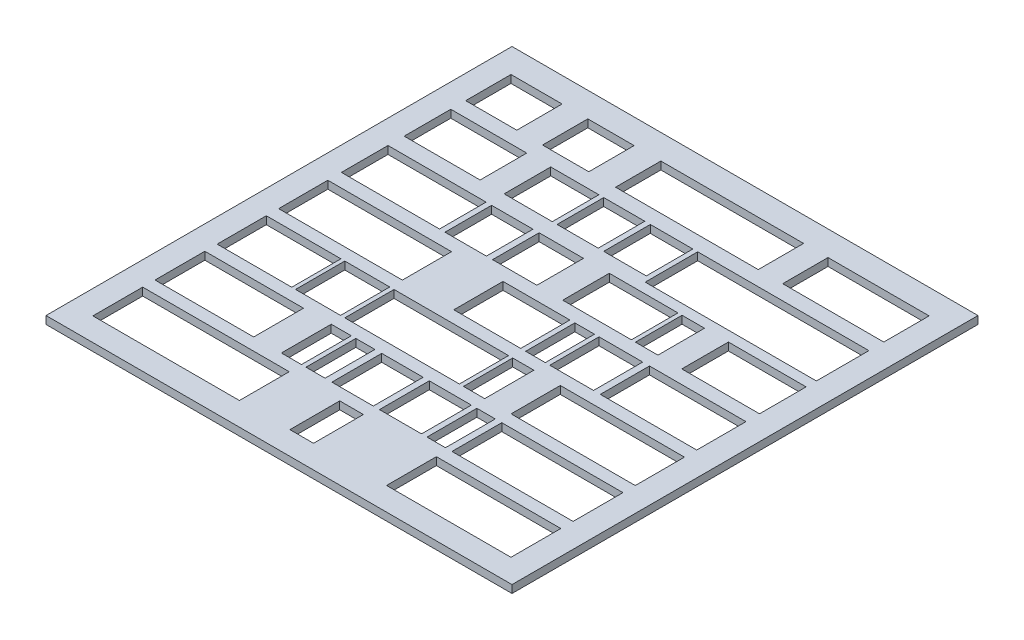
SolidWorks part; units mm, degrees
material "Maple"
ref_plane "Front Plane" through (0, 0, 0) normal (0, 0, 1) x (1, 0, 0)
ref_plane "Top Plane" through (0, 0, 0) normal (0, 1, 0) x (1, 0, 0)
ref_plane "Right Plane" through (0, 0, 0) normal (1, 0, 0) x (0, 0, -1)
sketch "Sketch1" plane through (0, 0, 0) normal (0, 1, 0) x (1, 0, 0)
  line L0 (-95.25, 95.25) -> (95.25, -95.25) construction
  line L1 (-95.25, 95.25) -> (95.25, 95.25)
  line L2 (-95.25, 95.25) -> (-95.25, -95.25)
  line L3 (-95.25, -95.25) -> (95.25, -95.25)
  line L4 (95.25, 95.25) -> (95.25, -95.25)
  dimension "D1" = 190.5
extrude "Boss-Extrude1" add sketch "Sketch1" along normal blind 3.175
sketch "Sketch4" plane through (0, 3.175, 0) normal (0, 1, 0) x (1, 0, 0)
  line L4 (-85.5388, 66.6005) -> (-64.6368, 66.6005)
  line L5 (-64.6368, 66.6005) -> (-64.6368, 85.1213)
  line L6 (-64.6368, 85.1213) -> (-85.5388, 85.1213)
  line L7 (-85.5388, 85.1213) -> (-85.5388, 66.6005)
  line L8 (-54.1196, 66.6005) -> (-35.202, 66.6005)
  line L9 (-35.202, 66.6005) -> (-35.202, 85.1213)
  line L10 (-35.202, 85.1213) -> (-54.1196, 85.1213)
  line L11 (-54.1196, 85.1213) -> (-54.1196, 66.6005)
  line L12 (-24.2702, 66.6005) -> (34.0704, 66.6005)
  line L13 (34.0704, 66.6005) -> (34.0704, 85.1213)
  line L14 (34.0704, 85.1213) -> (-24.2702, 85.1213)
  line L15 (-24.2702, 85.1213) -> (-24.2702, 66.6005)
  line L16 (44.0592, 66.6003) -> (85.382, 66.6003)
  line L17 (85.382, 66.6003) -> (85.382, 85.1213)
  line L18 (85.382, 85.1213) -> (44.0592, 85.1213)
  line L19 (44.0592, 85.1213) -> (44.0592, 66.6003)
  line L20 (-85.5388, 41.4648) -> (-54.4982, 41.4648)
  line L21 (-54.4982, 41.4648) -> (-54.4982, 60.515)
  line L22 (-54.4982, 60.515) -> (-85.5388, 60.515)
  line L23 (-85.5388, 60.515) -> (-85.5388, 41.4648)
  line L24 (-44.6805, 41.4648) -> (-24.9971, 41.4648)
  line L25 (-24.9971, 41.4648) -> (-24.9971, 60.515)
  line L26 (-24.9971, 60.515) -> (-44.6805, 60.515)
  line L27 (-44.6805, 60.515) -> (-44.6805, 41.4648)
  line L28 (-23.0273, 41.4648) -> (-6.2263, 41.4648)
  line L29 (-6.2263, 41.4648) -> (-6.2263, 60.515)
  line L30 (-6.2263, 60.515) -> (-23.0273, 60.515)
  line L31 (-23.0273, 60.515) -> (-23.0273, 41.4648)
  line L32 (-3.9772, 41.4648) -> (13.4192, 41.4648)
  line L33 (13.4192, 41.4648) -> (13.4192, 60.515)
  line L34 (13.4192, 60.515) -> (-3.9772, 60.515)
  line L35 (-3.9772, 60.515) -> (-3.9772, 41.4648)
  line L36 (15.4036, 39.0476) -> (85.382, 39.0476)
  line L37 (85.382, 39.0476) -> (85.382, 60.515)
  line L38 (85.382, 60.515) -> (15.4036, 60.515)
  line L39 (15.4036, 60.515) -> (15.4036, 39.0476)
  line L40 (34.661, 15.8004) -> (43.8468, 15.8004)
  line L41 (43.8468, 15.8004) -> (43.8468, 34.8504)
  line L42 (43.8468, 34.8504) -> (34.661, 34.8504)
  line L43 (34.661, 34.8504) -> (34.661, 15.8004)
  line L44 (-85.5388, 15.8004) -> (-45.4502, 15.8004)
  line L45 (-45.4502, 15.8004) -> (-45.4502, 34.8504)
  line L46 (-45.4502, 34.8504) -> (-85.5388, 34.8504)
  line L47 (-85.5388, 34.8504) -> (-85.5388, 15.8004)
  line L48 (-43.2012, 15.8004) -> (-26.2678, 15.8004)
  line L49 (-26.2678, 15.8004) -> (-26.2678, 34.8504)
  line L50 (-26.2678, 34.8504) -> (-43.2012, 34.8504)
  line L51 (-43.2012, 34.8504) -> (-43.2012, 15.8004)
  line L52 (-23.7543, 15.8004) -> (-5.6303, 15.8004)
  line L53 (-5.6303, 15.8004) -> (-5.6303, 34.8504)
  line L54 (-5.6303, 34.8504) -> (-23.7543, 34.8504)
  line L55 (-23.7543, 34.8504) -> (-23.7543, 15.8004)
  line L56 (4.9289, 15.8004) -> (32.9989, 15.8004)
  line L57 (32.9989, 15.8004) -> (32.9989, 34.8504)
  line L58 (32.9989, 34.8504) -> (4.9289, 34.8504)
  line L59 (4.9289, 34.8504) -> (4.9289, 15.8004)
  line L60 (53.6122, 15.8004) -> (85.382, 15.8004)
  line L61 (85.382, 15.8004) -> (85.382, 34.8504)
  line L62 (85.382, 34.8504) -> (53.6122, 34.8504)
  line L63 (53.6122, 34.8504) -> (53.6122, 15.8004)
  line L64 (-85.5388, -9.8641) -> (-34.9574, -9.8641)
  line L65 (-34.9574, -9.8641) -> (-34.9574, 10.2441)
  line L66 (-34.9574, 10.2441) -> (-85.5388, 10.2441)
  line L67 (-85.5388, 10.2441) -> (-85.5388, -9.8641)
  line L68 (-13.9229, -9.8641) -> (13.4195, -9.8641)
  line L69 (13.4195, -9.8641) -> (13.4195, 10.2441)
  line L70 (13.4195, 10.2441) -> (-13.9229, 10.2441)
  line L71 (-13.9229, 10.2441) -> (-13.9229, -9.8641)
  line L72 (15.4458, -9.8641) -> (23.4738, -9.8641)
  line L73 (23.4738, -9.8641) -> (23.4738, 10.2441)
  line L74 (23.4738, 10.2441) -> (15.4458, 10.2441)
  line L75 (15.4458, 10.2441) -> (15.4458, -9.8641)
  line L76 (45.9634, -9.8641) -> (85.382, -9.8641)
  line L77 (85.382, -9.8641) -> (85.382, 10.2441)
  line L78 (85.382, 10.2441) -> (45.9634, 10.2441)
  line L79 (45.9634, 10.2441) -> (45.9634, -9.8641)
  line L80 (25.3259, -9.8641) -> (43.1853, -9.8641)
  line L81 (43.1853, -9.8641) -> (43.1853, 10.2441)
  line L82 (43.1853, 10.2441) -> (25.3259, 10.2441)
  line L83 (25.3259, 10.2441) -> (25.3259, -9.8641)
  line L84 (-85.5388, -34.9997) -> (-55.0418, -34.9997)
  line L85 (-55.0418, -34.9997) -> (-55.0418, -14.8913)
  line L86 (-55.0418, -14.8913) -> (-85.5388, -14.8913)
  line L87 (-85.5388, -14.8913) -> (-85.5388, -34.9997)
  line L88 (-53.4782, -34.9997) -> (-35.09, -34.9997)
  line L89 (-35.09, -34.9997) -> (-35.09, -14.8913)
  line L90 (-35.09, -14.8913) -> (-53.4782, -14.8913)
  line L91 (-53.4782, -14.8913) -> (-53.4782, -34.9997)
  line L92 (-33.3458, -34.9997) -> (13.4858, -34.9997)
  line L93 (13.4858, -34.9997) -> (13.4858, -14.8913)
  line L94 (13.4858, -14.8913) -> (-33.3458, -14.8913)
  line L95 (-33.3458, -14.8913) -> (-33.3458, -34.9997)
  line L96 (15.1725, -34.9997) -> (23.8377, -34.9997)
  line L97 (23.8377, -34.9997) -> (23.8377, -14.8913)
  line L98 (23.8377, -14.8913) -> (15.1725, -14.8913)
  line L99 (15.1725, -14.8913) -> (15.1725, -34.9997)
  line L100 (34.6281, -34.9997) -> (85.3821, -34.9997)
  line L101 (85.3821, -34.9997) -> (85.3821, -14.8913)
  line L102 (85.3821, -14.8913) -> (34.6281, -14.8913)
  line L103 (34.6281, -14.8913) -> (34.6281, -34.9997)
  line L104 (-85.5388, -60.3996) -> (-45.2102, -60.3996)
  line L105 (-45.2102, -60.3996) -> (-45.2102, -40.0268)
  line L106 (-45.2102, -40.0268) -> (-85.5388, -40.0268)
  line L107 (-85.5388, -40.0268) -> (-85.5388, -60.3996)
  line L108 (-33.8741, -60.3996) -> (-25.6721, -60.3996)
  line L109 (-25.6721, -60.3996) -> (-25.6721, -40.0268)
  line L110 (-25.6721, -40.0268) -> (-33.8741, -40.0268)
  line L111 (-33.8741, -40.0268) -> (-33.8741, -60.3996)
  line L112 (-13.2366, -60.3996) -> (3.6968, -60.3996)
  line L113 (3.6968, -60.3996) -> (3.6968, -40.0268)
  line L114 (3.6968, -40.0268) -> (-13.2366, -40.0268)
  line L115 (-13.2366, -40.0268) -> (-13.2366, -60.3996)
  line L116 (-23.8199, -60.3996) -> (-16.0147, -60.3996)
  line L117 (-16.0147, -60.3996) -> (-16.0147, -40.0268)
  line L118 (-16.0147, -40.0268) -> (-23.8199, -40.0268)
  line L119 (-23.8199, -40.0268) -> (-23.8199, -60.3996)
  line L120 (6.2103, -60.3996) -> (23.4083, -60.3996)
  line L121 (23.4083, -60.3996) -> (23.4083, -40.0268)
  line L122 (23.4083, -40.0268) -> (6.2103, -40.0268)
  line L123 (6.2103, -40.0268) -> (6.2103, -60.3996)
  line L124 (25.6572, -60.3996) -> (33.1978, -60.3996)
  line L125 (33.1978, -60.3996) -> (33.1978, -40.0268)
  line L126 (33.1978, -40.0268) -> (25.6572, -40.0268)
  line L127 (25.6572, -40.0268) -> (25.6572, -60.3996)
  line L128 (35.8437, -60.3996) -> (85.3821, -60.3996)
  line L129 (85.3821, -60.3996) -> (85.3821, -40.0268)
  line L130 (85.3821, -40.0268) -> (35.8437, -40.0268)
  line L131 (35.8437, -40.0268) -> (35.8437, -60.3996)
  line L132 (-85.5388, -85.7996) -> (-25.6312, -85.7996)
  line L133 (-25.6312, -85.7996) -> (-25.6312, -65.4268)
  line L134 (-25.6312, -65.4268) -> (-85.5388, -65.4268)
  line L135 (-85.5388, -65.4268) -> (-85.5388, -85.7996)
  line L136 (-4.9935, -85.7996) -> (4.6637, -85.7996)
  line L137 (4.6637, -85.7996) -> (4.6637, -65.4268)
  line L138 (4.6637, -65.4268) -> (-4.9935, -65.4268)
  line L139 (-4.9935, -65.4268) -> (-4.9935, -85.7996)
  line L140 (34.521, -85.7996) -> (85.382, -85.7996)
  line L141 (85.382, -85.7996) -> (85.382, -65.4268)
  line L142 (85.382, -65.4268) -> (34.521, -65.4268)
  line L143 (34.521, -65.4268) -> (34.521, -85.7996)
extrude "Cut-Extrude2" cut sketch "Sketch4" against normal through all
